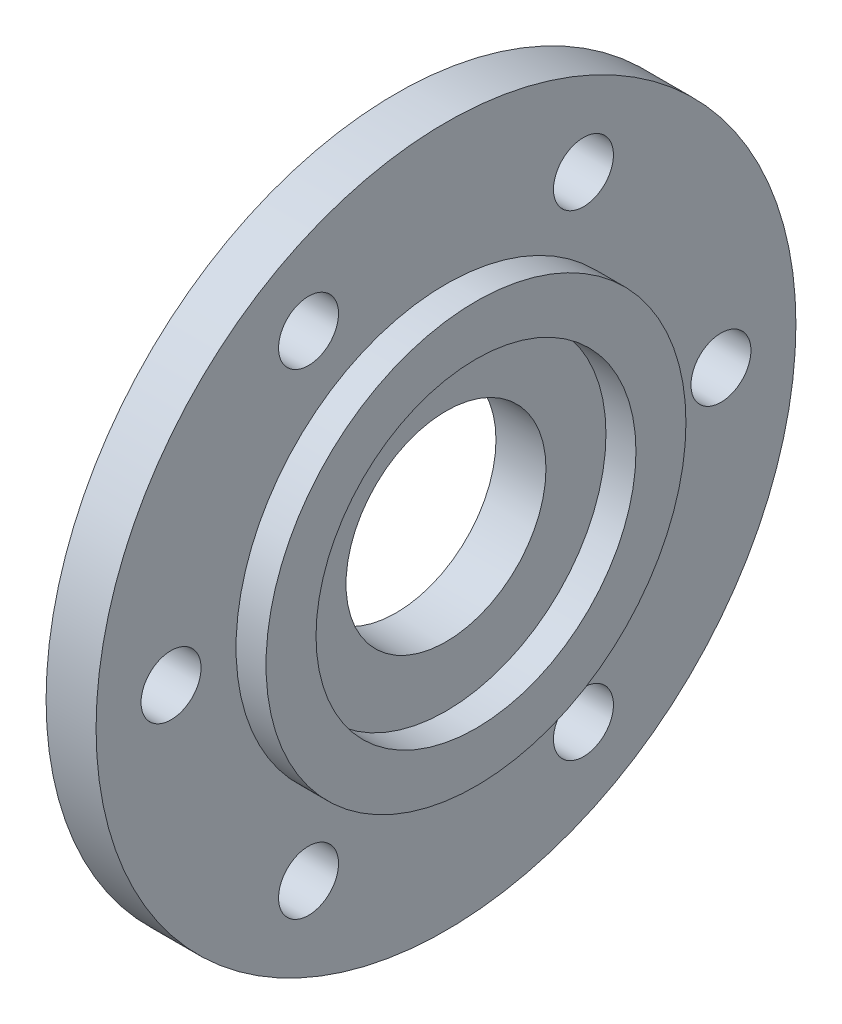
SolidWorks part; units mm, degrees
ref_plane "Front Plane" through (0, 0, 0) normal (0, 0, 1) x (1, 0, 0)
ref_plane "Top Plane" through (0, 0, 0) normal (0, 1, 0) x (1, 0, 0)
ref_plane "Right Plane" through (0, 0, 0) normal (1, 0, 0) x (0, 0, -1)
sketch "Sketch1" plane through (0, 0, 0) normal (0, 0, 1) x (1, 0, 0)
  line L0 (0, 35) -> (5, 35)
  line L1 (5, 35) -> (5, 21)
  line L2 (5, 21) -> (8, 21)
  line L3 (8, 21) -> (8, 16)
  line L4 (8, 16) -> (5, 16)
  line L5 (5, 16) -> (5, 0)
  line L6 (5, 0) -> (0, 0)
  line L7 (0, 0) -> (0, 35)
  dimension "D1" = 35
  dimension "D2" = 5
  dimension "D3" = 3
  dimension "D4" = 3
  dimension "D5" = 5
  dimension "D6" = 21
revolve "Revolve1" add sketch "Sketch1" angle 360 about L6
sketch "Sketch2" plane through (5, 0, 0) normal (1, 0, 0) x (0, 0, -1)
  circle A0 centre (0, 0) radius 27.5 construction
  circle A1 centre (27.5, 0) radius 3
  dimension "D1" = 55
  dimension "D2" = 6
extrude "Cut-Extrude1" cut sketch "Sketch2" against normal blind 10
pattern_circular "CirPattern1" count 6 over 360 about axis through (0, 0, 0) along (1, 0, 0) of "Cut-Extrude1"
sketch "Sketch3" plane through (5, 0, 0) normal (1, 0, 0) x (0, 0, -1)
  circle A0 centre (0, 0) radius 10
  dimension "D1" = 20
extrude "Cut-Extrude2" cut sketch "Sketch3" against normal blind 10
